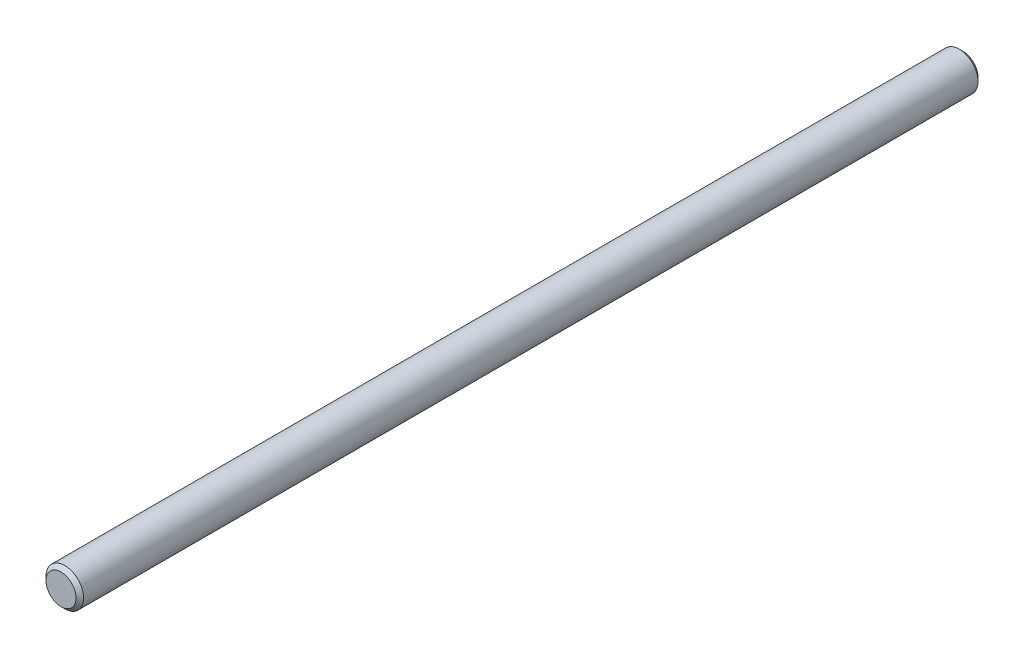
SolidWorks part; units mm, degrees
ref_plane "Front" through (0, 0, 0) normal (0, 0, 1) x (1, 0, 0)
ref_plane "Top" through (0, 0, 0) normal (0, 1, 0) x (1, 0, 0)
ref_plane "Right" through (0, 0, 0) normal (1, 0, 0) x (0, 0, -1)
sketch "Sketch1" plane through (0, 0, 0) normal (0, 0, 1) x (1, 0, 0)
  circle A0 centre (0, 0) radius 3.175 construction
  dimension "Diameter" = 6.35
sketch "Sketch2" plane through (0, 0, 0) normal (1, 0, 0) x (0, 0, -1)
  line L0 (-76.2, 0) -> (76.2, 0) construction
  line L1 (5.2388, 0) -> (-5.2388, 0) construction
  line L3 (76.2, 3.175) -> (76.2, -3.175) construction
  line L4 (-76.2, 3.175) -> (-76.2, -3.175) construction
  line L5 (-68.2625, 3.175) -> (-68.2625, -3.175) construction
  line L6 (68.2625, 3.175) -> (68.2625, -3.175) construction
  point P6 (0, 0)
  point P10 (76.2, 0)
  point P13 (-76.2, 0)
  point P16 (-68.2625, 0)
  point P19 (68.2625, 0)
  dimension "D1" = 6.35
  dimension "Length" = 152.4
  dimension "D2" = 7.9375
  dimension "D3" = 7.9375
sketch "Sketch3" plane through (0, 0, 0) normal (0, 0, 1) x (1, 0, 0)
  line L0 (0, 3.175) -> (0, -3.175) construction
  circle A0 centre (0, 0) radius 3.175
  dimension "D1" = 6.35
extrude "Boss-Extrude1" add sketch "Sketch3" along normal mid plane 152.4
chamfer "Chamfer1" distance 0.635 angle 45 2 edges at (3.175, 0, -76.2) (3.175, 0, 76.2)
equation "\"D1@Sketch2\" = \"Diameter@Sketch1\""
equation "\"D1@Sketch3\" = \"Diameter@Sketch1\""
equation "\"D1@Boss-Extrude1\" = \"Length@Sketch2\""
equation "\"D1@Chamfer1\" = \"Diameter@Sketch1\" * .1"
equation "\"D2@Sketch2\"=\"Diameter@Sketch1\"*1.25"
equation "\"D3@Sketch2\"=\"D2@Sketch2\""
